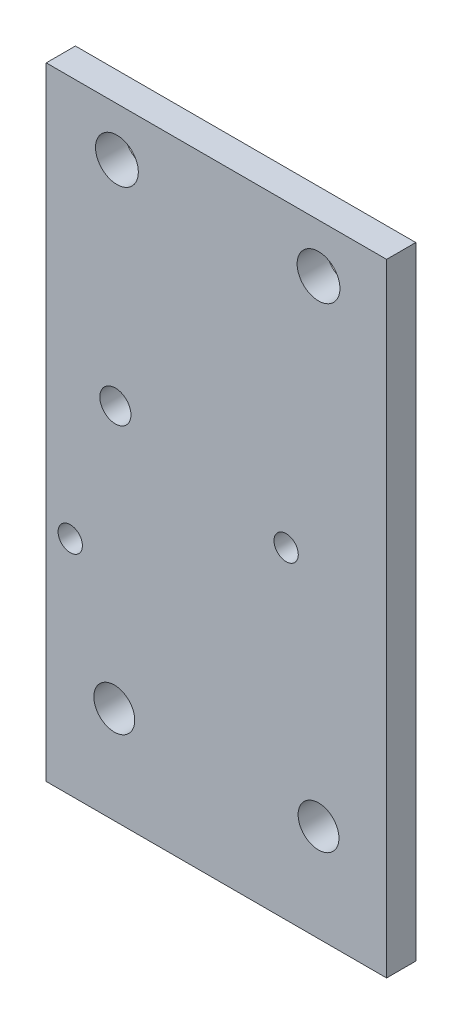
SolidWorks part; units mm, degrees
ref_plane "正面" through (0, 0, 0) normal (0, 0, 1) x (1, 0, 0)
ref_plane "平面" through (0, 0, 0) normal (0, 1, 0) x (1, 0, 0)
ref_plane "右側面" through (0, 0, 0) normal (1, 0, 0) x (0, 0, -1)
sketch "ｽｹｯﾁ1" plane through (0, 0, 0) normal (0, 0, 1) x (1, 0, 0)
  line L1 (-20, 14.5) -> (20, 14.5)
  line L2 (-20, 14.5) -> (-20, -14.5)
  line L3 (-20, -14.5) -> (20, -14.5)
  line L4 (20, 14.5) -> (20, -14.5)
  line L5 (-20, 14.5) -> (20, -14.5) construction
  line L6 (-20, -14.5) -> (20, 14.5) construction
  point P0 (0, 0)
  dimension "D1" = 40
  dimension "D2" = 29
extrude "ﾎﾞｽ - 押し出し1" add sketch "ｽｹｯﾁ1" along normal blind 3
sketch "ｽｹｯﾁ2" plane through (0, 0, 3) normal (0, 0, 1) x (1, 0, 0)
  line L1 (-20, 14.5) -> (-16.5, 14.5)
  line L2 (-20, 14.5) -> (-20, 10.5)
  line L3 (-20, 10.5) -> (-16.5, 10.5)
  line L4 (-16.5, 14.5) -> (-16.5, 10.5)
  line L5 (-20, -14.5) -> (-16.5, -14.5)
  line L6 (-20, -14.5) -> (-20, -10.5)
  line L7 (-20, -10.5) -> (-16.5, -10.5)
  line L8 (-16.5, -14.5) -> (-16.5, -10.5)
  line L9 (20, -14.5) -> (16.5, -14.5)
  line L10 (20, -14.5) -> (20, -10.5)
  line L11 (20, -10.5) -> (16.5, -10.5)
  line L12 (16.5, -14.5) -> (16.5, -10.5)
  line L13 (20, 14.5) -> (16.5, 14.5)
  line L14 (20, 14.5) -> (20, 10.5)
  line L15 (20, 10.5) -> (16.5, 10.5)
  line L16 (16.5, 14.5) -> (16.5, 10.5)
  circle A0 centre (-16.5, 10.5) radius 2.1
  circle A1 centre (-16.5, -10.5) radius 2.1
  circle A2 centre (16.5, -10.5) radius 2.1
  circle A3 centre (16.5, 10.5) radius 2.1
  dimension "D9" = 4.2
  dimension "D10" = 4.2
  dimension "D11" = 4.2
  dimension "D12" = 4.2
  dimension "D1" = 3.5
  dimension "D2" = 4
  dimension "D3" = 3.5
  dimension "D4" = 4
  dimension "D5" = 3.5
  dimension "D6" = 4
  dimension "D7" = 3.5
  dimension "D8" = 4
extrude "ｶｯﾄ - 押し出し1" cut sketch "ｽｹｯﾁ2" against normal blind 3 contours L3 A0 L4 | L4 A0 L3 | L8 A1 L7 | L7 A1 L8 | L12 A2 L11 | L11 A2 L12 | L16 A3 L15 | L15 A3 L16
sketch "ｽｹｯﾁ3" plane through (0, -14.5, 0) normal (0, -1, 0) x (1, 0, 0)
  line L1 (20, 0) -> (-20, 0)
  line L2 (20, 0) -> (20, 3)
  line L3 (20, 3) -> (-20, 3)
  line L4 (-20, 0) -> (-20, 3)
extrude "ﾎﾞｽ - 押し出し2" add sketch "ｽｹｯﾁ3" along normal blind 10
sketch "ｽｹｯﾁ4" plane through (0, 14.5, 0) normal (0, 1, 0) x (1, 0, 0)
  line L1 (20, -3) -> (-20, -3)
  line L2 (20, -3) -> (20, 0)
  line L3 (20, 0) -> (-20, 0)
  line L4 (-20, -3) -> (-20, 0)
extrude "ﾎﾞｽ - 押し出し3" add sketch "ｽｹｯﾁ4" along normal blind 10
sketch "ｽｹｯﾁ6" plane through (20, 0, 0) normal (1, 0, 0) x (0, 0, -1)
  line L1 (0, 24.5) -> (-3, 24.5)
  line L2 (0, 24.5) -> (0, -24.5)
  line L3 (0, -24.5) -> (-3, -24.5)
  line L4 (-3, 24.5) -> (-3, -24.5)
extrude "ﾎﾞｽ - 押し出し5" add sketch "ｽｹｯﾁ6" along normal blind 42
sketch "ｽｹｯﾁ7" plane through (0, 0, 3) normal (0, 0, 1) x (1, 0, 0)
  line L0 (62, 0) -> (43.1058, 0)
  line L1 (62, 24.5) -> (62, -24.5) construction
  line L2 (43.1058, 0) -> (36.1058, 0)
  line L7 (31.9689, -11.1369) -> (54.2427, 11.1369) construction
  line L8 (31.9689, 11.1369) -> (54.2427, -11.1369) construction
  line L9 (43.1058, 0) -> (29.4659, 7.875)
  line L10 (43.1058, 0) -> (43.1058, 15.75)
  line L11 (43.1058, 0) -> (56.7457, 7.875)
  line L12 (43.1058, 0) -> (29.4659, -7.875)
  line L13 (43.1058, 0) -> (43.1058, -15.75)
  line L14 (43.1058, 0) -> (56.7457, -7.875)
  circle A0 centre (43.1058, 0) radius 15.75
  circle A6 centre (43.1058, 15.75) radius 1.75
  circle A7 centre (29.4659, -7.875) radius 1.75
  circle A8 centre (43.1058, -15.75) radius 1.75
  circle A9 centre (56.7457, -7.875) radius 1.75
  circle A10 centre (56.7457, 7.875) radius 1.75
  circle A11 centre (36.1058, 0) radius 7
  dimension "D3" = 60
  dimension "D4" = 7
  dimension "D5" = 60
  dimension "D6" = 60
  dimension "D7" = 31.5
  dimension "D9" = 3.5
  dimension "D10" = 3.5
  dimension "D11" = 3.5
  dimension "D12" = 3.5
  dimension "D13" = 3.5
  dimension "D14" = 14
  dimension "D2" = 60
sketch "ｽｹｯﾁ8" plane through (-20, 0, 0) normal (-1, 0, 0) x (0, 0, 1)
  line L1 (3, -24.5) -> (0, -24.5)
  line L2 (3, -24.5) -> (3, 24.5)
  line L3 (3, 24.5) -> (0, 24.5)
  line L4 (0, -24.5) -> (0, 24.5)
extrude "ﾎﾞｽ - 押し出し6" add sketch "ｽｹｯﾁ8" along normal blind 2
sketch "ｽｹｯﾁ9" plane through (62, 0, 0) normal (1, 0, 0) x (0, 0, -1)
  line L1 (0, 24.5) -> (-3, 24.5)
  line L2 (0, 24.5) -> (0, -24.5)
  line L3 (0, -24.5) -> (-3, -24.5)
  line L4 (-3, 24.5) -> (-3, -24.5)
extrude "ﾎﾞｽ - 押し出し7" add sketch "ｽｹｯﾁ9" along normal blind 2
sketch "ｽｹｯﾁ10" plane through (0, -24.5, 0) normal (0, -1, 0) x (1, 0, 0)
  line L1 (-22, 0) -> (64, 0)
  line L2 (-22, 0) -> (-22, 3)
  line L3 (-22, 3) -> (64, 3)
  line L4 (64, 0) -> (64, 3)
extrude "ﾎﾞｽ - 押し出し8" add sketch "ｽｹｯﾁ10" along normal blind 10
sketch "ｽｹｯﾁ11" plane through (0, 24.5, 0) normal (0, 1, 0) x (1, 0, 0)
  line L1 (-22, 0) -> (64, 0)
  line L2 (-22, 0) -> (-22, -3)
  line L3 (-22, -3) -> (64, -3)
  line L4 (64, 0) -> (64, -3)
extrude "ﾎﾞｽ - 押し出し9" add sketch "ｽｹｯﾁ11" along normal blind 10
sketch "ｽｹｯﾁ14" plane through (-22, 0, 0) normal (-1, 0, 0) x (0, 0, 1)
  line L0 (0, 34.5) -> (0, -34.5) construction
  line L1 (3, -34.5) -> (0, -34.5)
  line L2 (3, -34.5) -> (3, 34.5)
  line L3 (3, 34.5) -> (0, 34.5)
  line L4 (0, -34.5) -> (0, 34.5)
  line L5 (0, 34.5) -> (3, 34.5) construction
extrude "ｶｯﾄ - 押し出し5" cut sketch "ｽｹｯﾁ14" against normal blind 43
sketch "ｽｹｯﾁ17" plane through (0, -34.5, 0) normal (0, -1, 0) x (1, 0, 0)
  line L1 (21, 3) -> (64, 3)
  line L2 (21, 3) -> (21, 0)
  line L3 (21, 0) -> (64, 0)
  line L4 (64, 3) -> (64, 0)
extrude "ﾎﾞｽ - 押し出し10" add sketch "ｽｹｯﾁ17" along normal blind 20
sketch "ｽｹｯﾁ18" plane through (0, 0, 3) normal (0, 0, 1) x (1, 0, 0)
  line L0 (21, -54.5) -> (21, -34.5)
  line L1 (21, -54.5) -> (21, 34.5) construction
  line L3 (64, -54.5) -> (64, -34.5)
  line L4 (64, 34.5) -> (64, -54.5) construction
  line L5 (64, -34.5) -> (57, -34.5)
  line L6 (21, -34.5) -> (36, -34.5)
  circle A0 centre (36, -34.5) radius 2.1
  circle A1 centre (57, -34.5) radius 2.1
  dimension "D5" = 4.2
  dimension "D6" = 4.2
  dimension "D1" = 20
  dimension "D2" = 20
  dimension "D3" = 7
  dimension "D4" = 15
extrude "ｶｯﾄ - 押し出し6" cut sketch "ｽｹｯﾁ18" against normal blind 10
sketch "ｽｹｯﾁ19" plane through (0, 0, 3) normal (0, 0, 1) x (1, 0, 0)
  line L0 (42.5, -54.5) -> (42.5, 34.5)
  line L1 (64, -54.5) -> (21, -54.5) construction
  line L2 (21, 34.5) -> (64, 34.5) construction
  circle A0 centre (36, -34.5) radius 2.1 construction
  circle A1 centre (57, -34.5) radius 2.1 construction
  dimension "D2" = 14.5
  dimension "D1" = 6.5
sketch "ｽｹｯﾁ20" plane through (0, -54.5, 0) normal (0, -1, 0) x (1, 0, 0)
  line L1 (64, 0) -> (21, 0)
  line L2 (64, 0) -> (64, 3)
  line L3 (64, 3) -> (21, 3)
  line L4 (21, 0) -> (21, 3)
extrude "ﾎﾞｽ - 押し出し11" add sketch "ｽｹｯﾁ20" along normal blind 10
sketch "ｽｹｯﾁ21" plane through (0, -64.5, 0) normal (0, -1, 0) x (1, 0, 0)
  line L1 (21, 3) -> (64, 3)
  line L2 (21, 3) -> (21, 0)
  line L3 (21, 0) -> (64, 0)
  line L4 (64, 3) -> (64, 0)
extrude "ｶｯﾄ - 押し出し7" cut sketch "ｽｹｯﾁ21" against normal blind 20
sketch "ｽｹｯﾁ24" plane through (0, 0, 0) normal (0, 0, -1) x (-1, 0, 0)
  line L0 (-42.5, 34.5) -> (-36.27, 34.5)
  line L1 (-64, 34.5) -> (-21, 34.5) construction
  line L2 (-36.27, 34.5) -> (-36.27, 14.5)
  line L3 (-64, 34.5) -> (-64, 14.5)
  line L4 (-64, -44.5) -> (-64, 34.5) construction
  line L5 (-64, 14.5) -> (-57, 14.5)
  circle A0 centre (-36.27, 14.5) radius 2.2
  circle A1 centre (-57, 14.5) radius 2.2
  dimension "D6" = 4.4
  dimension "D7" = 4.4
  dimension "D1" = 6.23
  dimension "D2" = 20
  dimension "D3" = 20
  dimension "D4" = 0
  dimension "D5" = 7
extrude "ｶｯﾄ - 押し出し8" cut sketch "ｽｹｯﾁ24" against normal blind 30
sketch "ｽｹｯﾁ25" plane through (0, 0, 0) normal (0, 0, -1) x (-1, 0, 0)
  line L0 (-21, 34.5) -> (-21, 31.5)
  line L1 (-21, 34.5) -> (-21, -44.5) construction
  line L2 (-21, 31.5) -> (-24, 31.5)
  line L3 (-24, 31.5) -> (-24, 16.9055)
  line L4 (-24, 16.9055) -> (-46.2, 16.9055)
  line L5 (-46.2, 16.9055) -> (-46.2, 27.2055)
  circle A0 centre (-24, 16.9055) radius 1.55
  circle A1 centre (-46.2, 27.2055) radius 1.55
  dimension "D5" = 3.1
  dimension "D6" = 3.1
  dimension "D1" = 3
  dimension "D2" = 3
  dimension "D3" = 22.2
  dimension "D4" = 10.3
sketch "ｽｹｯﾁ27" plane through (0, 0, 0) normal (0, 0, -1) x (-1, 0, 0)
  line L0 (-42.5, -44.5364) -> (-36.11, -44.5)
  line L2 (-42.5, -54.5) -> (-42.5, 34.5) construction
  line L3 (-21, -44.5) -> (-64, -44.5) construction
  line L4 (-36.11, -44.5) -> (-36.11, -7.5)
  circle A0 centre (-36.11, -7.5) radius 1.6
  dimension "D2" = 3.2
  dimension "D1" = 6.39
  dimension "D3" = 37
extrude "ｶｯﾄ - 押し出し9" cut sketch "ｽｹｯﾁ27" against normal blind 10
sketch "ｽｹｯﾁ28" plane through (21, 0, 0) normal (-1, 0, 0) x (0, 0, 1)
  line L1 (0, 34.5) -> (3, 34.5)
  line L2 (0, 34.5) -> (0, -44.5)
  line L3 (0, -44.5) -> (3, -44.5)
  line L4 (3, 34.5) -> (3, -44.5)
extrude "ｶｯﾄ - 押し出し10" cut sketch "ｽｹｯﾁ28" against normal blind 8
sketch "ｽｹｯﾁ29" plane through (0, 34.5, 0) normal (0, 1, 0) x (1, 0, 0)
  line L1 (29, -3) -> (64, -3)
  line L2 (29, -3) -> (29, 0)
  line L3 (29, 0) -> (64, 0)
  line L4 (64, -3) -> (64, 0)
extrude "ｶｯﾄ - 押し出し11" cut sketch "ｽｹｯﾁ29" against normal blind 15
sketch "ｽｹｯﾁ30" plane through (0, 0, 0) normal (0, 0, -1) x (-1, 0, 0)
  line L0 (-36.27, 14.5) -> (-36.27, 1.64)
  line L1 (-36.27, 1.64) -> (-31.74, 1.64)
  line L2 (-31.74, 1.64) -> (-31.74, -8.66)
  line L3 (-31.74, -8.66) -> (-53.94, -8.66)
  circle A0 centre (-31.74, 1.64) radius 1.9986
  circle A1 centre (-53.94, -8.66) radius 2.9583
  dimension "D1" = 12.86
  dimension "D2" = 4.53
  dimension "D3" = 10.3
  dimension "D4" = 22.2
sketch "ｽｹｯﾁ32" plane through (0, 0, 3) normal (0, 0, 1) x (1, 0, 0)
  line L0 (36, -34.5) -> (36, -21.64)
  line L1 (36, -21.64) -> (31.47, -21.64)
  line L2 (31.47, -21.64) -> (31.47, -11.34)
  line L3 (31.47, -11.34) -> (53.67, -11.34)
  circle A0 centre (31.47, -21.64) radius 2.3016
  circle A1 centre (53.67, -11.34) radius 2.5489
  dimension "D1" = 12.86
  dimension "D2" = 4.53
  dimension "D3" = 10.3
  dimension "D4" = 22.2
hole_wizard "M3x0.5 ねじ穴2" positions "3Dｽｹｯﾁ2" profile "ｽｹｯﾁ33" tap size "M3x0.5" standard "JIS"
sketch3d "3Dｽｹｯﾁ2"
  point P0 (31.47, -21.64, 3)
  point P3 (53.67, -11.34, 3)
sketch "ｽｹｯﾁ33" plane through (31.47, -21.64, 3) normal (1, 0, 0) x (0, -1, 0)
  line L0 (0, 0) -> (0, 9.2511)
  line L1 (0, 9.2511) -> (1.25, 8.5)
  line L2 (1.25, 8.5) -> (1.25, 0)
  line L5 (1.25, 0) -> (0, 0)
  line L10 (0, 9.2511) -> (-1.25, 8.5) construction
  line L11 (0, -6.35) -> (0, 107.95) construction
  dimension "ねじ下穴ﾄﾞﾘﾙ直径" = 2.5
  dimension "ねじ下穴ﾄﾞﾘﾙの深さ" = 8.5
  dimension "ﾄﾞﾘﾙ角度" = 118
cosmetic thread "穴のねじ山3" parameters "D1"=3, "D2"=3
cosmetic thread "穴のねじ山4" parameters "D1"=3, "D2"=3
